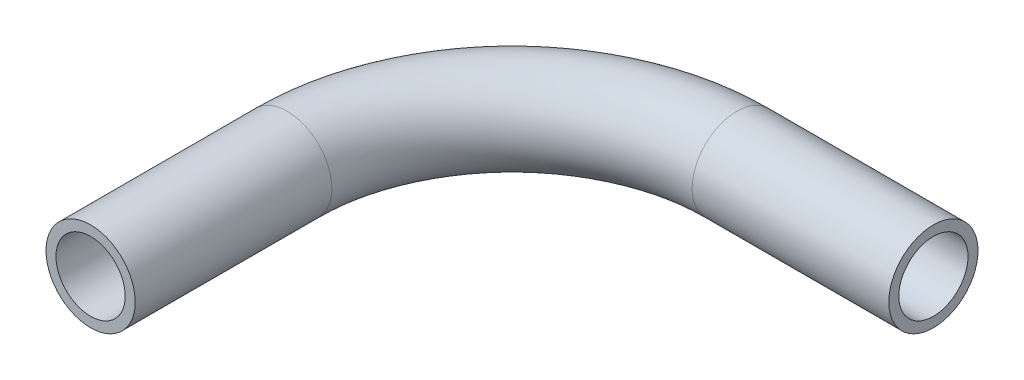
SolidWorks part; units mm, degrees
material "AISI 304"
ref_plane "Front Plane" through (0, 0, 0) normal (0, 0, 1) x (1, 0, 0)
ref_plane "Top Plane" through (0, 0, 0) normal (0, 1, 0) x (1, 0, 0)
ref_plane "Right Plane" through (0, 0, 0) normal (1, 0, 0) x (0, 0, -1)
sketch "Sketch1" plane through (0, 0, 0) normal (0, 1, 0) x (1, 0, 0)
  line L0 (0, 0) -> (0, 14)
  line L1 (16, 30) -> (17.2, 30)
  line L2 (17.2, 30) -> (30, 30)
  arc A1 (0, 14) -> (16, 30) centre (16, 14) cw
  dimension "D1" = 30
  dimension "D2" = 16
  dimension "D3" = 14
sketch "Sketch2" plane through (0, 0, 0) normal (0, 0, 1) x (1, 0, 0)
  circle A0 centre (0, 0) radius 3.175
  dimension "D1" = 6.35
sweep "Sweep-Thin1" add profiles "Sketch2" path "Sketch1" parameters "D1"=0.7112
